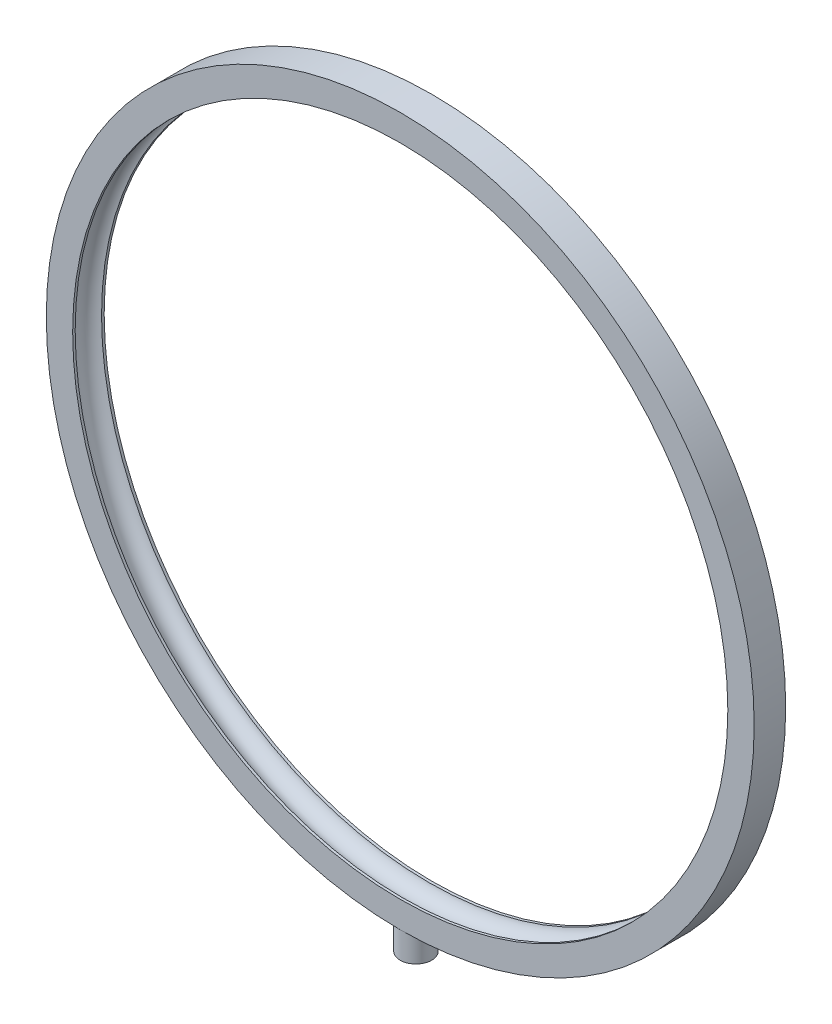
SolidWorks part; units mm, degrees
ref_plane "Front Plane" through (0, 0, 0) normal (0, 0, 1) x (1, 0, 0)
ref_plane "Top Plane" through (0, 0, 0) normal (0, 1, 0) x (1, 0, 0)
ref_plane "Right Plane" through (0, 0, 0) normal (1, 0, 0) x (0, 0, -1)
sketch "Sketch1" plane through (0, 0, 0) normal (1, 0, 0) x (0, 0, -1)
  line L1 (-5.9544, 124.2472) -> (-5.9544, 134.2472)
  line L3 (6, 134.2472) -> (6, 124.2472)
  line L4 (-5.9544, 124.2472) -> (-5, 124.2472)
  line L5 (6, 124.2472) -> (5, 124.2472)
  line L6 (-5.9544, 134.2472) -> (6, 134.2472)
  line L7 (-30.3023, 0) -> (12.7321, 0) construction
  arc A0 (5, 124.2472) -> (-5, 124.2472) centre (0, 123.1222) ccw
  point P0 (0, 124.2472)
  point P1 (0, 128.2472)
  point P5 (0, 124.2472)
  dimension "D1" = 124.2472
  dimension "D2" = 6
  dimension "D3" = 4
revolve "Revolve1" add sketch "Sketch1" angle 360 about L7
ref_plane "Plane1" through (0, -134.2472, 0) normal (0, -1, 0) x (-1, 0, 0)
sketch "Sketch3" plane through (0, -134.2472, 0) normal (0, -1, 0) x (-1, 0, 0)
  circle A0 centre (0, 0) radius 5.975
extrude "Boss-Extrude1" add sketch "Sketch3" along normal blind 10 separate body contours A0
